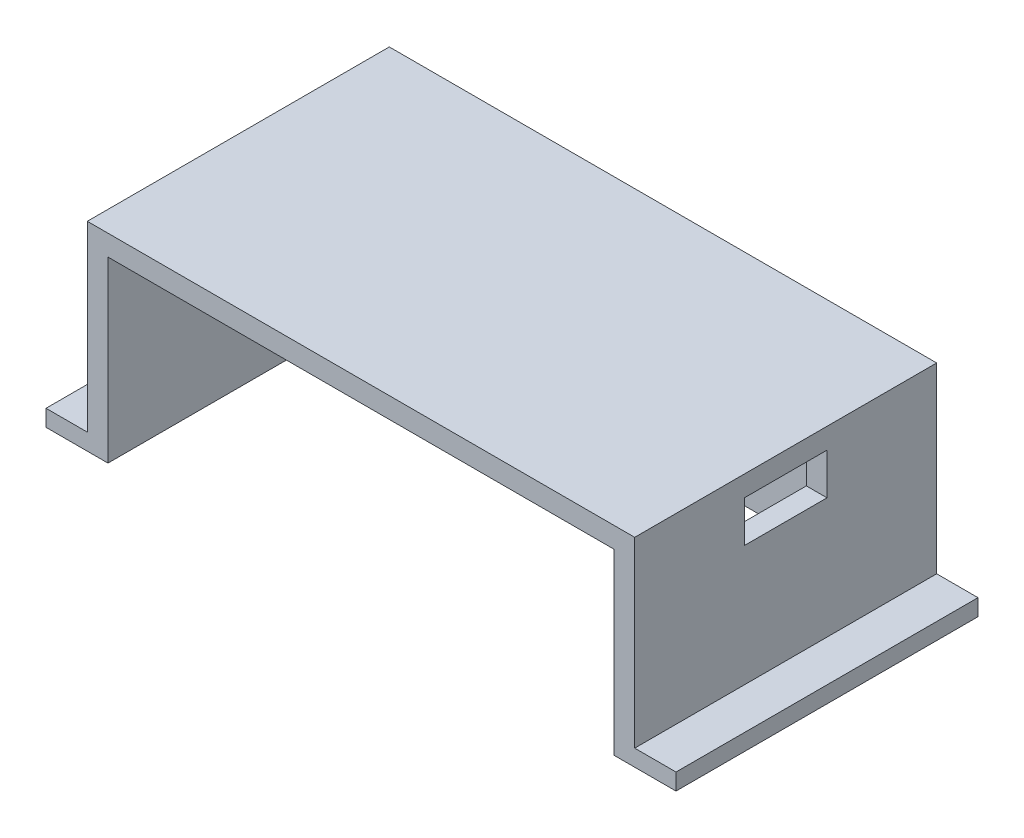
SolidWorks part; units mm, degrees
ref_plane "前基準面" through (0, 0, 0) normal (0, 0, 1) x (1, 0, 0)
ref_plane "上基準面" through (0, 0, 0) normal (0, 1, 0) x (1, 0, 0)
ref_plane "右基準面" through (0, 0, 0) normal (1, 0, 0) x (0, 0, -1)
sketch "草圖1" plane through (0, 0, 0) normal (0, 1, 0) x (1, 0, 0)
  line L1 (-66.25, 36.55) -> (66.25, 36.55)
  line L2 (-66.25, 36.55) -> (-66.25, -36.55)
  line L3 (-66.25, -36.55) -> (66.25, -36.55)
  line L4 (66.25, 36.55) -> (66.25, -36.55)
  line L5 (0, -36.55) -> (0, 36.55) construction
  line L6 (-66.25, 0) -> (66.25, 0) construction
  point P1 (0, 0)
  dimension "D1" = 132.5
  dimension "D2" = 73.1
extrude "填料-伸長1" add sketch "草圖1" along normal blind 48.2 contours L1 L4 L3 L2
sketch "草圖3" plane through (0, 0, 36.55) normal (0, 0, 1) x (1, 0, 0)
  line L0 (-66.25, 0) -> (66.25, 0) construction
  line L1 (-61.25, 0) -> (61.25, 0)
  line L2 (-61.25, 0) -> (-61.25, 43.2)
  line L3 (-61.25, 43.2) -> (61.25, 43.2)
  line L4 (61.25, 0) -> (61.25, 43.2)
  line L5 (-66.25, 48.2) -> (-66.25, 0) construction
  dimension "D1" = 122.5
  dimension "D2" = 5
  dimension "D3" = 43.2
extrude "除料-伸長1" cut sketch "草圖3" against normal blind 68.1
sketch "草圖7" plane through (66.25, 0, 0) normal (1, 0, 0) x (0, 0, -1)
  line L0 (36.55, 48.2) -> (-36.55, 48.2) construction
  line L1 (-10, 43.2) -> (10, 43.2)
  line L2 (-10, 43.2) -> (-10, 33.2)
  line L3 (-10, 33.2) -> (10, 33.2)
  line L4 (10, 43.2) -> (10, 33.2)
  line L5 (0, 33.2) -> (0, 43.2) construction
  line L6 (-10, 38.2) -> (10, 38.2) construction
  line L8 (0, 0) -> (0, 48.2) construction
  line L9 (36.55, 0) -> (-36.55, 0) construction
  point P0 (0, 38.2)
  dimension "D1" = 5
  dimension "D2" = 20
  dimension "D3" = 10
  dimension "D4" = 0
extrude "除料-伸長2" cut sketch "草圖7" against normal blind 10
sketch "草圖8" plane through (66.25, 0, 0) normal (1, 0, 0) x (0, 0, -1)
  line L0 (36.55, 48.2) -> (36.55, 0) construction
  line L1 (-36.55, 0) -> (36.55, 0)
  line L2 (-36.55, 0) -> (-36.55, 4)
  line L3 (-36.55, 4) -> (36.55, 4)
  line L4 (36.55, 0) -> (36.55, 4)
  dimension "D1" = 4
extrude "填料-伸長2" add sketch "草圖8" along normal blind 10
sketch "草圖9" plane through (-66.25, 0, 0) normal (-1, 0, 0) x (0, 0, 1)
  line L0 (36.55, 48.2) -> (36.55, 0) construction
  line L1 (-36.55, 0) -> (36.55, 0)
  line L2 (-36.55, 0) -> (-36.55, 4)
  line L3 (-36.55, 4) -> (36.55, 4)
  line L4 (36.55, 0) -> (36.55, 4)
  dimension "D1" = 4
extrude "填料-伸長3" add sketch "草圖9" along normal blind 10
